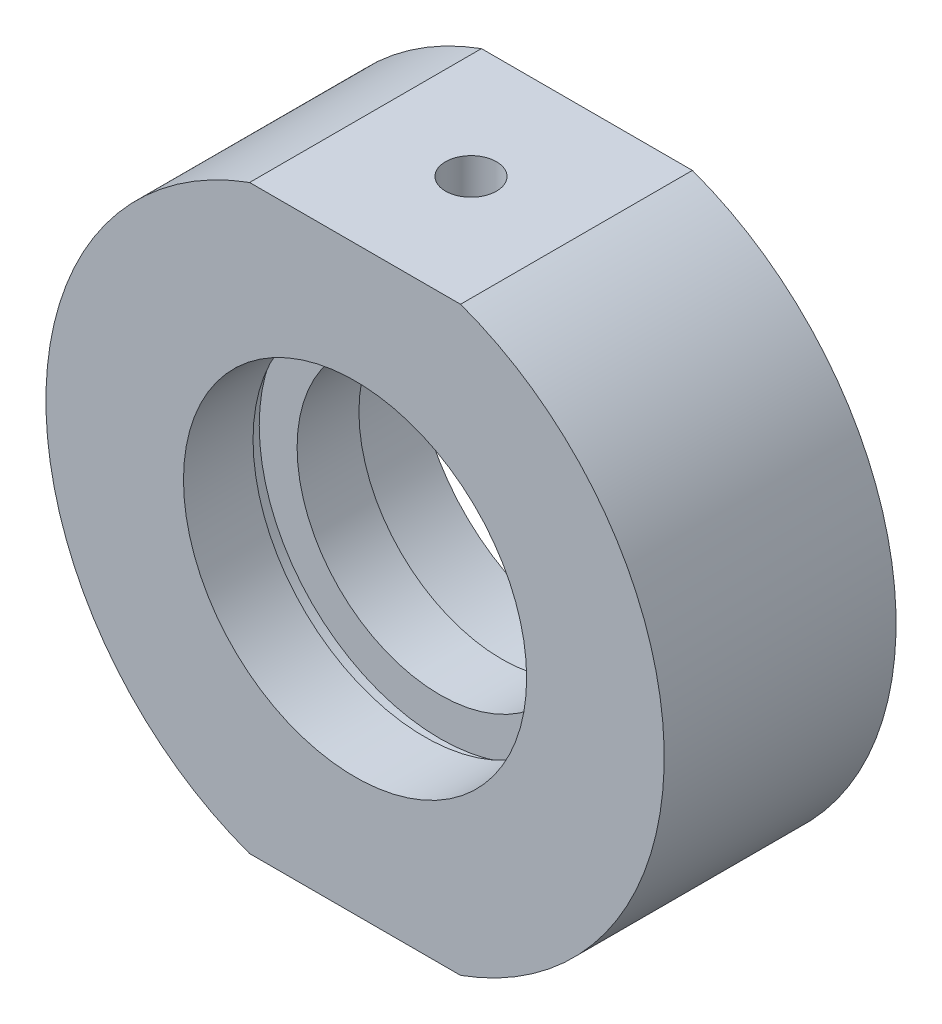
SolidWorks part; units mm, degrees
ref_plane "前视基准面" through (0, 0, 0) normal (0, 0, 1) x (1, 0, 0)
ref_plane "上视基准面" through (0, 0, 0) normal (0, 1, 0) x (1, 0, 0)
ref_plane "右视基准面" through (0, 0, 0) normal (1, 0, 0) x (0, 0, -1)
sketch "草图1" plane through (0, 0, 0) normal (0, 1, 0) x (1, 0, 0)
  line L0 (0, 31.9391) -> (0, -26.491) construction
  line L1 (20, 7.5) -> (20, -7.5)
  line L3 (11.7, 2) -> (11.7, 3)
  line L4 (11.7, 3) -> (11.1, 3)
  line L6 (20, -7.5) -> (11.1, -7.5)
  line L7 (11.1, -7.5) -> (11.1, -3)
  line L8 (11.7, -2) -> (9.25, -2)
  line L9 (9.25, -2) -> (9.25, 2)
  line L10 (9.25, 2) -> (11.7, 2)
  line L11 (11.1, 3) -> (11.1, 7.5)
  line L12 (11.1, 7.5) -> (20, 7.5)
  line L13 (11.7, -2) -> (11.7, -3)
  line L14 (11.7, -3) -> (11.1, -3)
  line L17 (35.331, 0) -> (-5.0345, 0) construction
  point P6 (9.25, 0)
  dimension "D2" = 9.25
  dimension "D3" = 11.1
  dimension "D4" = 11.1
  dimension "D5" = 15
  dimension "D6" = 5.5
  dimension "D7" = 5.5
  dimension "D8" = 11.7
  dimension "D9" = 20
  dimension "D10" = 11.7
  dimension "D11" = 1
  dimension "D12" = 1
  dimension "D13" = 7.5
  dimension "D18" = 0
revolve "旋转1" add sketch "草图1" angle 360 about L0
cosmetic thread "装饰螺纹线1" parameters "D2"=23.2
cosmetic thread "装饰螺纹线2" parameters "D2"=23.2
sketch "草图2" plane through (0, 0, 7.5) normal (0, 0, 1) x (1, 0, 0)
  line L0 (0, 0) -> (43.1523, 0) construction
  line L1 (-33.152, 28.0489) -> (30.8698, 28.0489)
  line L2 (-33.152, 28.0489) -> (-33.152, 18.8)
  line L3 (-33.152, 18.8) -> (30.8698, 18.8)
  line L4 (30.8698, 28.0489) -> (30.8698, 18.8)
  line L5 (30.8698, -28.0489) -> (30.8698, -18.8)
  line L6 (-33.152, -18.8) -> (30.8698, -18.8)
  line L7 (-33.152, -28.0489) -> (-33.152, -18.8)
  line L8 (-33.152, -28.0489) -> (30.8698, -28.0489)
  dimension "D1" = 18.8
extrude "切除-拉伸1" cut sketch "草图2" against normal blind 49
sketch "草图10" plane through (0, 0, 0) normal (0, 0, 1) x (1, 0, 0)
  line L0 (0, 18.8) -> (0, -18.8)
  line L1 (-6.8235, 18.8) -> (6.8235, 18.8) construction
  line L2 (-6.8235, -18.8) -> (6.8235, -18.8) construction
  line L3 (0, 0) -> (-17.3205, 10)
  line L4 (0, 0) -> (17.3205, 10)
  arc A2 (6.8235, -18.8) -> (6.8235, 18.8) centre (0, 0) ccw construction
  arc A3 (-6.8235, 18.8) -> (-6.8235, -18.8) centre (0, 0) ccw construction
  arc A4 (17.3205, 10) -> (6.8235, 18.8) centre (0, 0) ccw
  arc A5 (-6.8235, 18.8) -> (-17.3205, 10) centre (0, 0) ccw
  dimension "D1" = 60
  dimension "D2" = 60
hole_wizard "M4 螺纹孔2" positions "草图15" profile "草图16" tap size "M4" standard "ISO"
sketch "草图15" plane through (0, 18.8, 0) normal (0, 1, 0) x (1, 0, 0)
  point P0 (0, 0)
sketch "草图16" plane through (0, 18.8, 0) normal (1, 0, 0) x (0, 0, 1)
  line L0 (0, 0) -> (0, 6.4914)
  line L1 (0, 6.4914) -> (1.65, 5.5)
  line L2 (1.65, 5.5) -> (1.65, 0)
  line L5 (1.65, 0) -> (0, 0)
  line L10 (0, 6.4914) -> (-1.65, 5.5) construction
  line L11 (0, -6.35) -> (0, 107.95) construction
  dimension "螺纹孔钻头直径" = 3.3
  dimension "螺纹孔钻头深度" = 5.5
  dimension "导头角度" = 118
cosmetic thread "孔螺蚊线6" parameters "D1"=5.5, "D2"=4
hole_wizard "M6 螺纹孔2" positions "草图17" profile "草图18" tap size "M6" standard "ISO"
sketch "草图17" plane through (0, -18.8, 0) normal (0, -1, 0) x (-1, 0, 0)
  point P0 (0, 0)
sketch "草图18" plane through (0, -18.8, 0) normal (1, 0, 0) x (0, 0, -1)
  line L0 (0, 0) -> (0, 7.0022)
  line L1 (0, 7.0022) -> (2.5, 5.5)
  line L2 (2.5, 5.5) -> (2.5, 0)
  line L5 (2.5, 0) -> (0, 0)
  line L10 (0, 7.0022) -> (-2.5, 5.5) construction
  line L11 (0, -6.35) -> (0, 107.95) construction
  dimension "螺纹孔钻头直径" = 5
  dimension "螺纹孔钻头深度" = 5.5
  dimension "导头角度" = 118
cosmetic thread "孔螺蚊线7" parameters "D1"=5.5, "D2"=6
